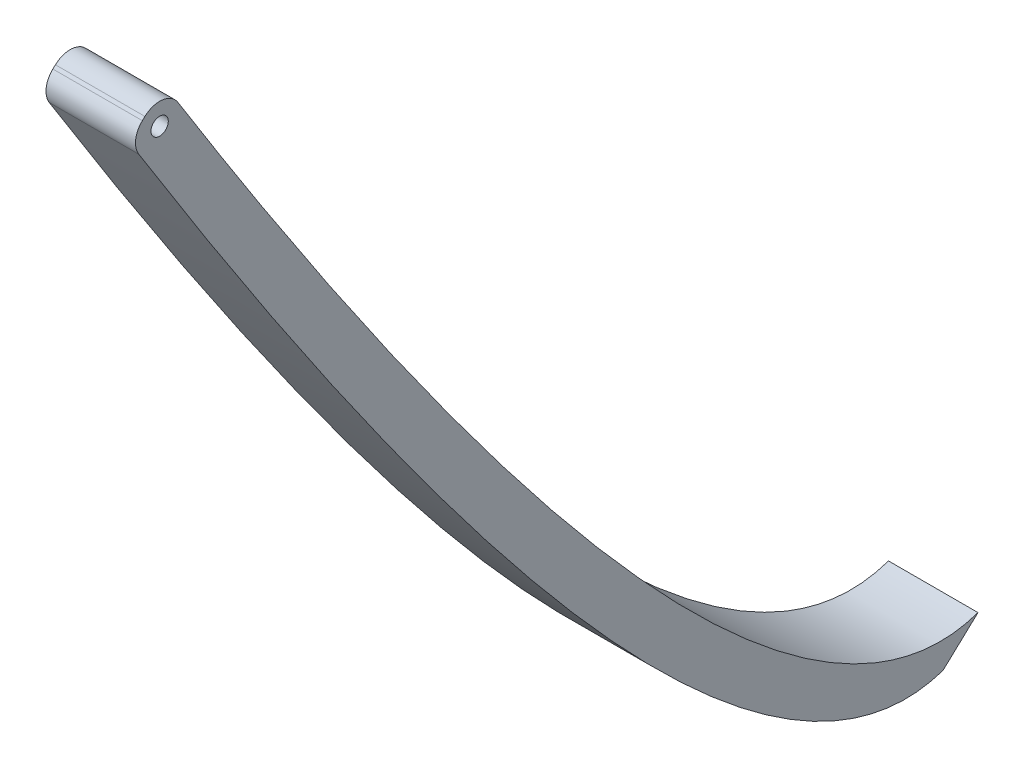
SolidWorks part; units mm, degrees
ref_plane "Front Plane" through (0, 0, 0) normal (0, 0, 1) x (1, 0, 0)
ref_plane "Top Plane" through (0, 0, 0) normal (0, 1, 0) x (1, 0, 0)
ref_plane "Right Plane" through (0, 0, 0) normal (1, 0, 0) x (0, 0, -1)
sketch "Sketch3" plane through (0, 0, 0) normal (1, 0, 0) x (0, 0, -1)
  line L0 (0, 0) -> (4.0889, 3.8087)
  line L1 (95.694, -101.6) -> (99.783, -97.7913)
  spline S0 degree 2 poles (-7.5724, 12.362) (74.4899, -123.2238) (100.6465, -98.5229) knots 0 0 0 1 1 1 construction
  spline S1 degree 2 poles (0, 0) (68.833, -110.9687) (95.694, -101.6) knots 0.046887 0.046887 0.046887 0.913353 0.913353 0.913353
  spline S2 degree 2 poles (-3.4834, 16.1707) (78.5788, -119.415) (104.7354, -94.7142) knots 0 0 0 1 1 1 construction
  spline S3 degree 2 poles (4.0889, 3.8087) (72.9219, -107.16) (99.783, -97.7913) knots 0.046887 0.046887 0.046887 0.913353 0.913353 0.913353
  dimension "D1" = 101.6
  dimension "D2" = 5.588
extrude "Boss-Extrude1" add sketch "Sketch3" along normal blind 10.5207
fillet "Fillet1" radius 2.54 2 edges at (5.2603, 0, 0) (5.2603, 3.8087, -4.0889)
sketch "Sketch5" plane through (0, 0, 0) normal (-1, 0, 0) x (0, 0, 1)
  circle A0 centre (-3.5621, -0.1532) radius 1.016
  dimension "D1" = 2.032
extrude "Cut-Extrude2" cut sketch "Sketch5" against normal blind 10.5207
